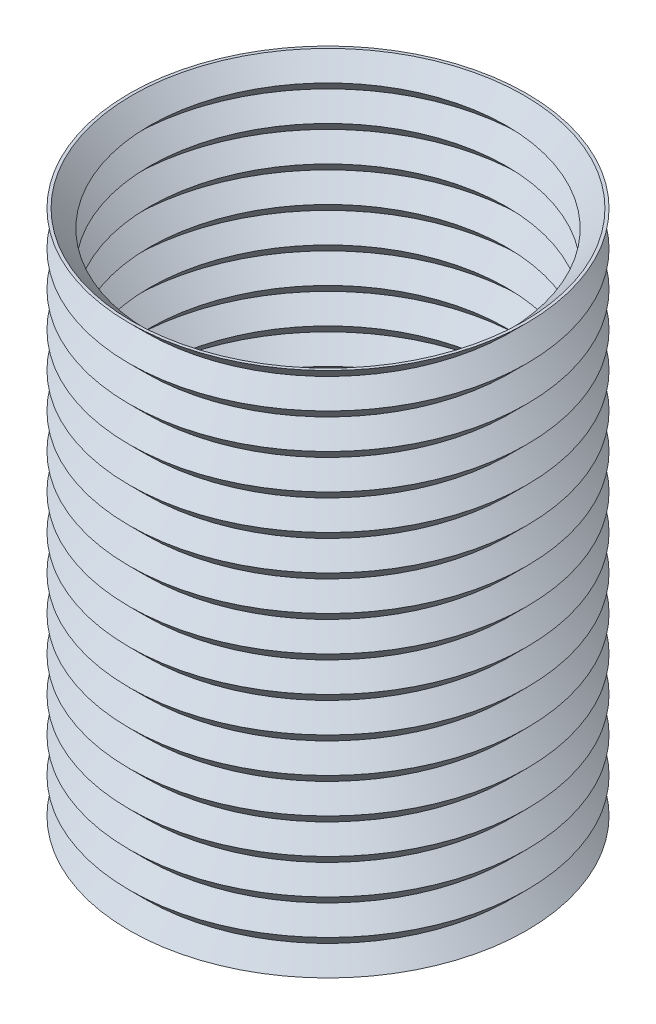
SolidWorks part; units mm, degrees
ref_plane "Płaszczyzna przednia" through (0, 0, 0) normal (0, 0, 1) x (1, 0, 0)
ref_plane "Płaszczyzna górna" through (0, 0, 0) normal (0, 1, 0) x (1, 0, 0)
ref_plane "Płaszczyzna prawa" through (0, 0, 0) normal (1, 0, 0) x (0, 0, -1)
sketch "Szkic1" plane through (0, 0, 0) normal (0, 0, 1) x (1, 0, 0)
  line L0 (0, 39.7381) -> (0, 0) construction
  line L1 (68, 0) -> (62, 6)
  line L12 (68, 0) -> (0, 0)
  line L13 (0, 0) -> (0, 180)
  line L15 (62, 6) -> (68, 12)
  line L16 (68, 12) -> (62, 18)
  line L17 (62, 18) -> (68, 24)
  line L18 (68, 24) -> (62, 30)
  line L19 (62, 30) -> (68, 36)
  line L20 (68, 36) -> (62, 42)
  line L21 (62, 42) -> (68, 48)
  line L22 (68, 48) -> (62, 54)
  line L23 (62, 54) -> (68, 60)
  line L24 (68, 60) -> (62, 66)
  line L25 (62, 66) -> (68, 72)
  line L26 (68, 72) -> (62, 78)
  line L27 (62, 78) -> (68, 84)
  line L28 (68, 84) -> (62, 90)
  line L29 (62, 90) -> (68, 96)
  line L30 (68, 96) -> (62, 102)
  line L31 (62, 102) -> (68, 108)
  line L32 (68, 108) -> (62, 114)
  line L33 (62, 114) -> (68, 120)
  line L35 (68, 120) -> (62, 126)
  line L36 (62, 126) -> (68, 132)
  line L38 (68, 132) -> (62, 138)
  line L39 (62, 138) -> (68, 144)
  line L40 (68, 144) -> (62, 150)
  line L41 (62, 150) -> (68, 156)
  line L42 (68, 156) -> (62, 162)
  line L43 (62, 162) -> (68, 168)
  line L44 (68, 168) -> (62, 174)
  line L45 (62, 174) -> (68, 180)
  line L46 (68, 180) -> (0, 180)
  dimension "D1" = 68
  dimension "D3" = 12
  dimension "D4" = 15
revolve "Obrót1" add sketch "Szkic1" angle 360 about L0
shell "Skorupa1" thickness 0.7
